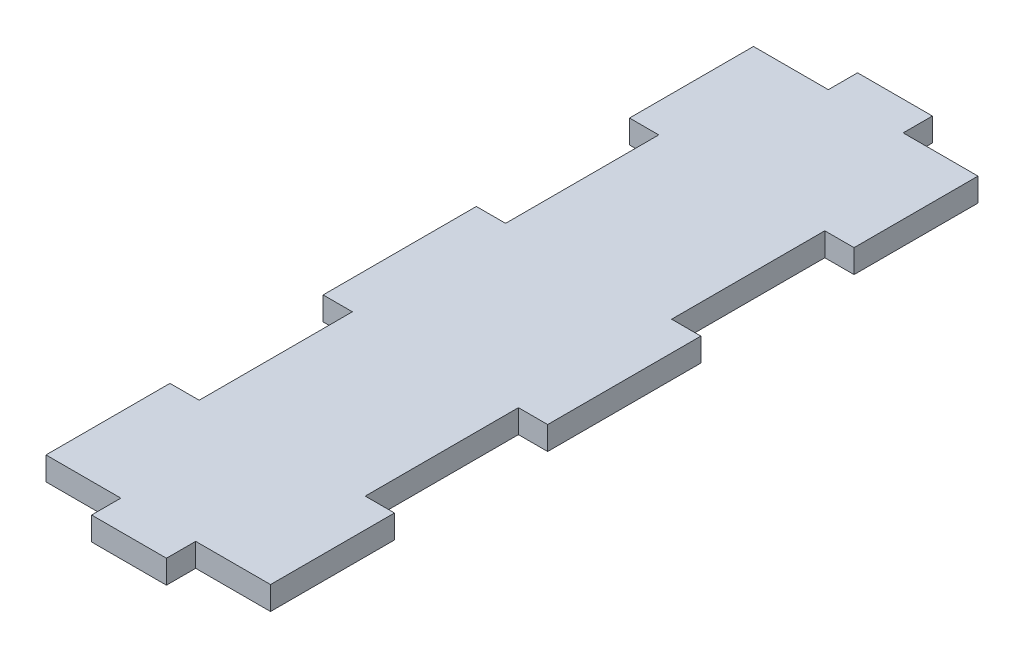
SolidWorks part; units mm, degrees
ref_plane "Front Plane" through (0, 0, 0) normal (0, 0, 1) x (1, 0, 0)
ref_plane "Top Plane" through (0, 0, 0) normal (0, 1, 0) x (1, 0, 0)
ref_plane "Right Plane" through (0, 0, 0) normal (1, 0, 0) x (0, 0, -1)
sketch "Sketch1" plane through (0, 0, 0) normal (0, 1, 0) x (1, 0, 0)
  line L1 (-12.192, -41.5925) -> (12.192, -41.5925)
  line L2 (-12.192, -41.5925) -> (-12.192, 41.5925)
  line L3 (-12.192, 41.5925) -> (12.192, 41.5925)
  line L4 (12.192, -41.5925) -> (12.192, 41.5925)
  line L5 (-12.192, -41.5925) -> (12.192, 41.5925) construction
  line L6 (-12.192, 41.5925) -> (12.192, -41.5925) construction
  point P0 (0, 0)
  dimension "D1" = 24.384
  dimension "D2" = 83.185
extrude "Boss-Extrude1" add sketch "Sketch1" along normal blind 2.54
sketch "Sketch2" plane through (0, 2.54, 0) normal (0, 1, 0) x (1, 0, 0)
  line L0 (-12.192, 41.5925) -> (-12.192, -41.5925) construction
  line L1 (12.192, -41.5925) -> (12.192, 41.5925) construction
  line L2 (-15.367, -8.3185) -> (-9.017, -8.3185) construction
  line L3 (-15.367, -8.3185) -> (-15.367, 8.3185) construction
  line L4 (-15.367, 8.3185) -> (-9.017, 8.3185) construction
  line L5 (-9.017, -8.3185) -> (-9.017, 8.3185) construction
  line L6 (-15.367, -8.3185) -> (-9.017, 8.3185) construction
  line L7 (-15.367, 8.3185) -> (-9.017, -8.3185) construction
  line L8 (-9.017, 8.3185) -> (-12.192, 8.3185)
  line L9 (-9.017, 8.3185) -> (-9.017, 24.9555)
  line L10 (-9.017, 24.9555) -> (-12.192, 24.9555)
  line L11 (-12.192, 8.3185) -> (-12.192, 24.9555)
  line L12 (12.192, 8.3185) -> (9.017, 8.3185)
  line L13 (12.192, 8.3185) -> (12.192, 24.9555)
  line L14 (12.192, 24.9555) -> (9.017, 24.9555)
  line L15 (9.017, 8.3185) -> (9.017, 24.9555)
  point P3 (-12.192, 0)
  dimension "D1" = 6.35
  dimension "D2" = 16.637
  dimension "D3" = 16.637
  dimension "D4" = 3.175
extrude "Cut-Extrude1" cut sketch "Sketch2" against normal blind 2.54
pattern_linear "LPattern1" count 2 spacing 33.274 along (0, 0, 1) of "Cut-Extrude1"
sketch "Sketch3" plane through (0, 2.54, 0) normal (0, 1, 0) x (1, 0, 0)
  line L1 (4.064, 38.4175) -> (12.192, 38.4175)
  line L2 (4.064, 38.4175) -> (4.064, 41.5925)
  line L3 (4.064, 41.5925) -> (12.192, 41.5925)
  line L4 (12.192, 38.4175) -> (12.192, 41.5925)
  line L5 (12.192, -41.5925) -> (4.064, -41.5925)
  line L6 (12.192, -41.5925) -> (12.192, -38.4175)
  line L7 (12.192, -38.4175) -> (4.064, -38.4175)
  line L8 (4.064, -41.5925) -> (4.064, -38.4175)
  dimension "D1" = 8.128
  dimension "D2" = 3.175
  dimension "D3" = 3.175
extrude "Cut-Extrude5" cut sketch "Sketch3" against normal blind 3.175
pattern_linear "LPattern3" count 2 spacing 16.256 along (-1, 0, 0) of "Cut-Extrude5"
